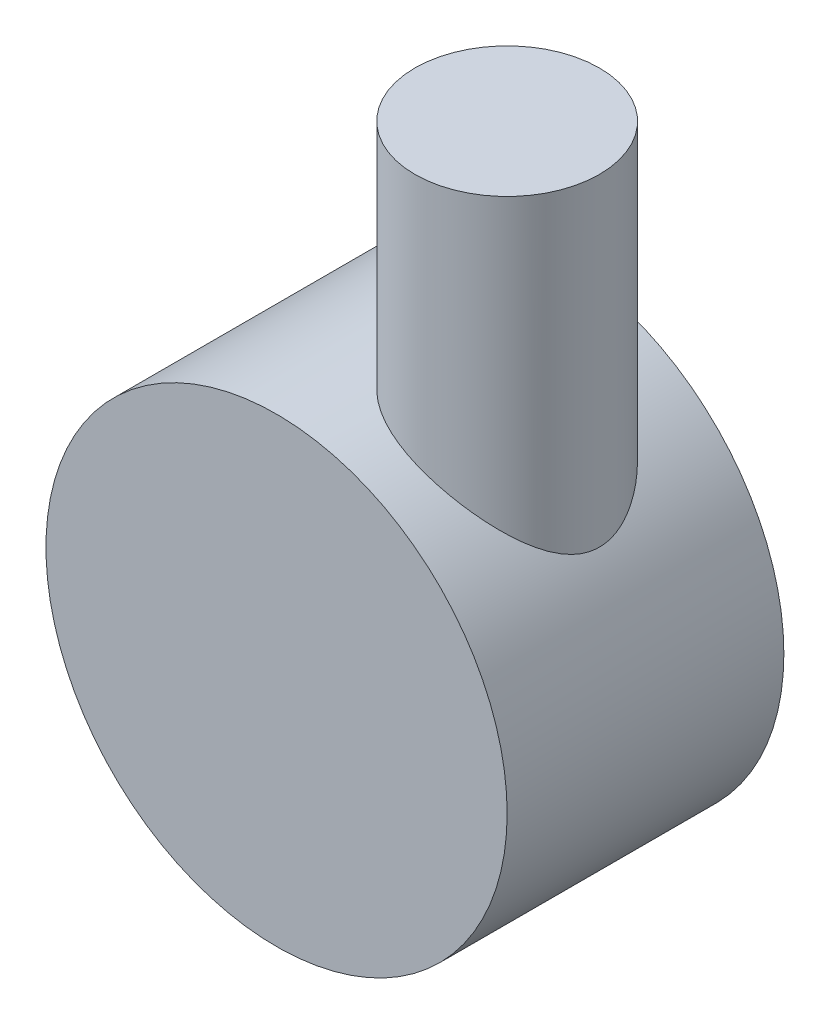
SolidWorks part; units mm, degrees
ref_plane "Front Plane" through (0, 0, 0) normal (0, 0, 1) x (1, 0, 0)
ref_plane "Top Plane" through (0, 0, 0) normal (0, 1, 0) x (1, 0, 0)
ref_plane "Right Plane" through (0, 0, 0) normal (1, 0, 0) x (0, 0, -1)
sketch "Sketch1" plane through (0, 0, 0) normal (0, 0, 1) x (1, 0, 0)
  circle A0 centre (0, 0) radius 25
extrude "Boss-Extrude1" add sketch "Sketch1" along normal blind 30
sketch "Sketch2" plane through (0, 0, 0) normal (0, 1, 0) x (1, 0, 0)
  circle A0 centre (10, -15) radius 10
extrude "Boss-Extrude2" add sketch "Sketch2" along normal blind 50
